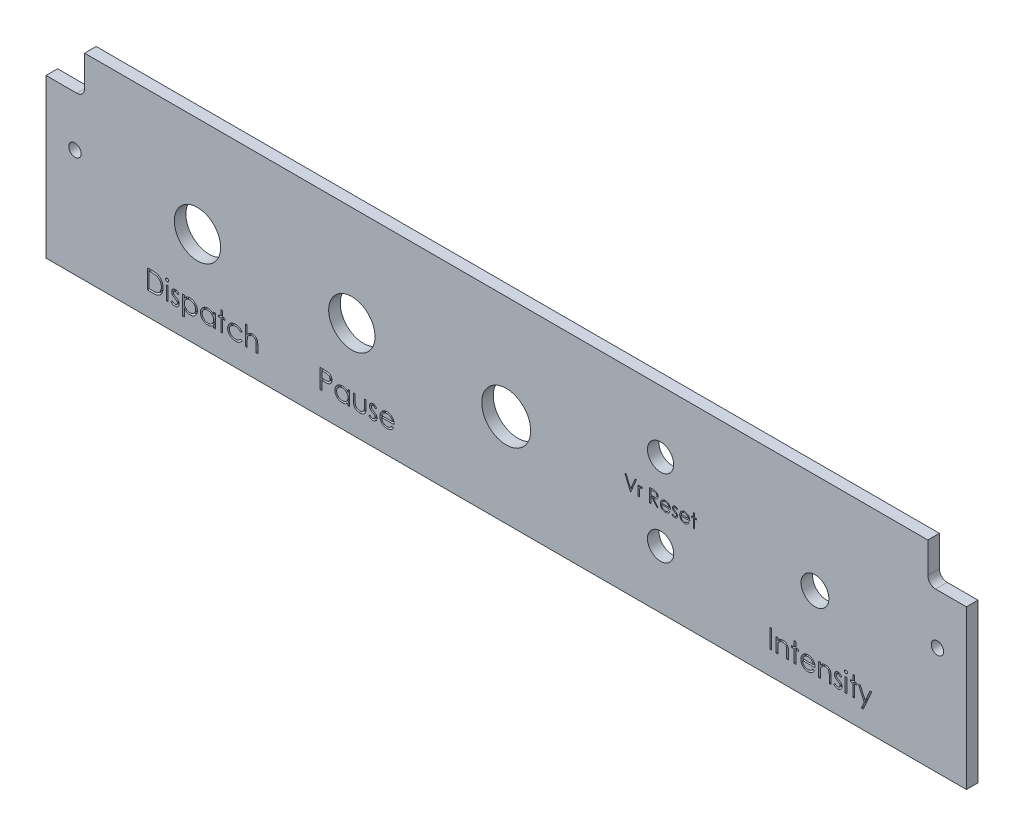
SolidWorks part; units mm, degrees
ref_plane "Front Plane" through (0, 0, 0) normal (0, 0, 1) x (1, 0, 0)
ref_plane "Top Plane" through (0, 0, 0) normal (0, 1, 0) x (1, 0, 0)
ref_plane "Right Plane" through (0, 0, 0) normal (1, 0, 0) x (0, 0, -1)
sketch "Sketch1" plane through (0, 0, 0) normal (0, 0, 1) x (1, 0, 0)
  line L0 (-9.0872, -71.8857) -> (-5.6872, -71.8857) construction
  line L7 (-9.0872, -51.8857) -> (-9.0872, -71.8857) construction
  line L8 (-117.9874, -61.8857) -> (-89.0872, -61.8857) construction
  line L9 (60.1628, -45.8857) -> (-185.5426, -45.8857) construction
  line L10 (-160.8372, -37.7868) -> (-160.8372, -58.8857) construction
  line L11 (-49.0872, -86.8857) -> (-49.0872, -35.8857) construction
  line L13 (62.6628, -37.7868) -> (62.6628, -60.4857) construction
  line L16 (-158.3372, -35.8857) -> (60.1628, -35.8857)
  line L19 (-168.3372, -45.8857) -> (-168.3372, -86.8857)
  line L25 (70.1628, -45.8857) -> (70.1628, -86.8857)
  line L26 (-168.3372, -45.8857) -> (-160.3372, -45.8857)
  line L29 (-168.3372, -35.8857) -> (-158.3372, -35.8857) construction
  line L38 (-168.3372, -35.8857) -> (-168.3372, -47.1743) construction
  line L39 (-158.3372, -43.8857) -> (-158.3372, -35.8857)
  line L40 (62.1628, -45.8857) -> (70.1628, -45.8857)
  line L41 (60.1628, -43.8857) -> (60.1628, -35.8857)
  line L42 (-168.3372, -86.8857) -> (70.1628, -86.8857)
  circle A0 centre (-129.0872, -61.8857) radius 6
  circle A1 centre (-89.0872, -61.8857) radius 6
  circle A2 centre (-49.0872, -62.8299) radius 6.35
  circle A3 centre (-9.0872, -71.8857) radius 3.4
  circle A4 centre (30.9128, -61.8857) radius 3.6
  arc A6 (62.1628, -45.8857) -> (60.1628, -43.8857) centre (62.1628, -43.8857) cw
  circle A9 centre (62.6628, -58.8857) radius 1.6
  circle A10 centre (-160.8372, -58.8857) radius 1.6
  circle A12 centre (-9.0872, -51.8857) radius 3.4
  arc A13 (-160.3372, -45.8857) -> (-158.3372, -43.8857) centre (-160.3372, -43.8857) ccw
  point P28 (62.6628, -58.8857)
  point P37 (-160.8372, -58.8857)
  dimension "D1" = 3.2
  dimension "D20" = 2
  dimension "D21" = 3.2
  dimension "D3" = 25
  dimension "D6" = 109.25
  dimension "D7" = 109.25
  dimension "D8" = 7.5
  dimension "D9" = 7.5
  dimension "D10" = 25
  dimension "D11" = 20
  dimension "D12" = 15
  dimension "D13" = 40
  dimension "D14" = 40
  dimension "D15" = 80
  dimension "D16" = 40
  dimension "D2" = 51
  dimension "D4" = 39.7113
  dimension "D17" = 119.25
  dimension "D5" = 119.25
  dimension "D18" = 28
  dimension "D19" = 28
extrude "Boss-Extrude2" add sketch "Sketch1" along normal blind 3
sketch "Sketch2" plane through (0, 0, 3) normal (0, 0, 1) x (1, 0, 0)
  line L0 (-127.8375, -61.8857) -> (-127.8375, -80.8857) construction
  line L1 (-107.5236, -80.8857) -> (-68.1514, -80.8857) construction
  line L2 (-87.8375, -61.8857) -> (-87.8375, -80.8857) construction
  line L3 (-9.0872, -71.8857) -> (-9.0872, -63.6357) construction
  line L4 (-147.5236, -80.8857) -> (-108.1514, -80.8857) construction
  line L5 (1.6919, -63.6357) -> (-19.8663, -63.6357) construction
  line L6 (12.4764, -80.8857) -> (51.8486, -80.8857) construction
  line L7 (32.1625, -61.8857) -> (32.1625, -80.8857) construction
  text T0 "Dispatch" font "Century Gothic" height 5
  text T1 "Pause" font "Century Gothic" height 5
  text T2 "Intensity" font "Century Gothic" height 5
  text T3 "Vr Reset"
  point P6 (-83.8375, -80.8857)
  point P11 (-47.8383, -81.8218)
  point P14 (-127.8375, -80.8857)
  point P17 (-83.8375, -80.3477)
  point P20 (32.1625, -80.8857)
  point P24 (-9.0872, -63.6357)
  dimension "D1" = 19
extrude "Cut-Extrude1" cut sketch "Sketch2" against normal blind 1
equation "\"panel_height\"= 51"
equation "\"D2@Sketch1\"=\"panel_height\""
equation "\"width\" = 238.5"
equation "\"D17@Sketch1\"= \"width\" /2"
equation "\"D5@Sketch1\"= \"width\" /2"
